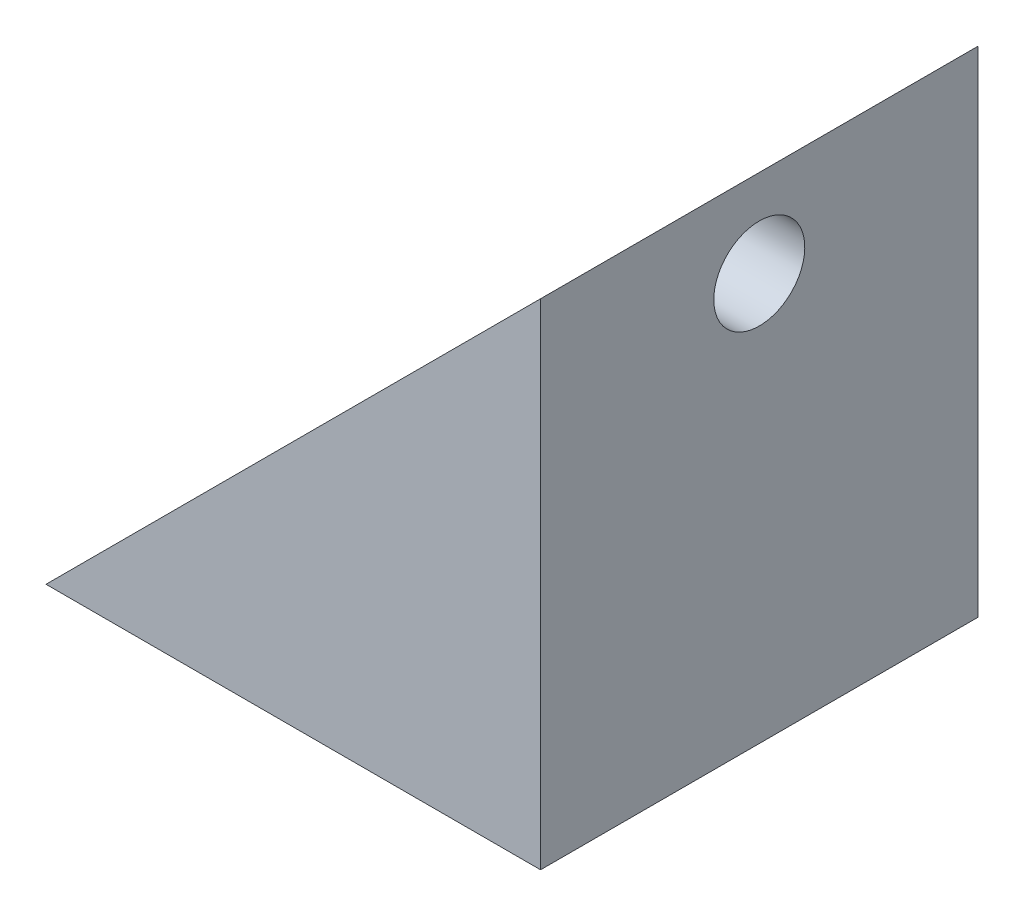
SolidWorks part; units mm, degrees
ref_plane "Front Plane" through (0, 0, 0) normal (0, 0, 1) x (1, 0, 0)
ref_plane "Top Plane" through (0, 0, 0) normal (0, 1, 0) x (1, 0, 0)
ref_plane "Right Plane" through (0, 0, 0) normal (1, 0, 0) x (0, 0, -1)
sketch "Sketch1" plane through (0, 0, 0) normal (0, 0, 1) x (1, 0, 0)
  line L0 (0, 0) -> (28.2657, 28.2657)
  line L1 (28.2657, 28.2657) -> (28.2657, 0)
  line L2 (28.2657, 0) -> (0, 0)
  dimension "D1" = 45
  dimension "D2" = 28.2657
extrude "Boss-Extrude1" add sketch "Sketch1" against normal blind 25
sketch "Sketch2" plane through (0, 0, 0) normal (0, -1, 0) x (1, 0, 0)
  line L0 (20, -25) -> (20, 0) construction
  line L1 (0, 0) -> (28.2657, 0) construction
  line L2 (0, -25) -> (28.2657, -25) construction
  line L3 (20, -12.5) -> (0, -12.5) construction
  line L4 (0, -12.5) -> (0, 0) construction
  line L5 (10, -12.5) -> (0, -12.5) construction
  line L6 (5, -12.5) -> (5, 0) construction
  circle A1 centre (5, -12.5) radius 2.6
  dimension "D1" = 5.2
  dimension "D2" = 5
extrude "Cut-Extrude1" cut sketch "Sketch2" against normal through all
sketch "Sketch3" plane through (28.2657, 0, 0) normal (1, 0, 0) x (0, 0, -1)
  line L0 (12.5, 28.2657) -> (12.5, 8.2657) construction
  line L1 (25, 28.2657) -> (0, 28.2657) construction
  line L3 (12.5, 18.2657) -> (12.5, 28.2657) construction
  line L4 (25, 0) -> (25, 28.2657) construction
  line L5 (12.5, 23.2657) -> (25, 23.2657) construction
  line L6 (25, 28.2657) -> (25, 0) construction
  circle A1 centre (12.5, 23.2657) radius 2.6
  dimension "D1" = 5.2
  dimension "D2" = 5
extrude "Cut-Extrude2" cut sketch "Sketch3" against normal up to surface and the other way through all up to face at (2.4, 2.4, -12.5)
sketch "Sketch5" plane through (28.2657, 0, 0) normal (1, 0, 0) x (0, 0, -1)
  circle A0 centre (12.5, 23.2657) radius 5.5
  dimension "D2" = 11
extrude "Cut-Extrude3" cut sketch "Sketch5" along direction (1, 0, 0) on the side against the normal through all from offset 4 offset against normal yes
sketch "Sketch7" plane through (0, 0, 0) normal (0, -1, 0) x (1, 0, 0)
  circle A0 centre (5, -12.5) radius 5.5
  dimension "D1" = 11
extrude "Cut-Extrude4" cut sketch "Sketch7" against normal through all from offset 4 offset against normal yes
sketch "Sketch9" plane through (28.2657, 0, 0) normal (1, 0, 0) x (0, 0, -1)
  line L0 (25, 28.2657) -> (25, 0) construction
  line L1 (0, 28.2657) -> (25, 28.2657)
  line L2 (0, 28.2657) -> (0, 24.2657)
  line L3 (0, 24.2657) -> (25, 24.2657)
  line L4 (25, 28.2657) -> (25, 24.2657)
  dimension "D1" = 4
extrude "Cut-Extrude5" [suppressed] cut sketch "Sketch9" against normal up to surface and the other way through all
